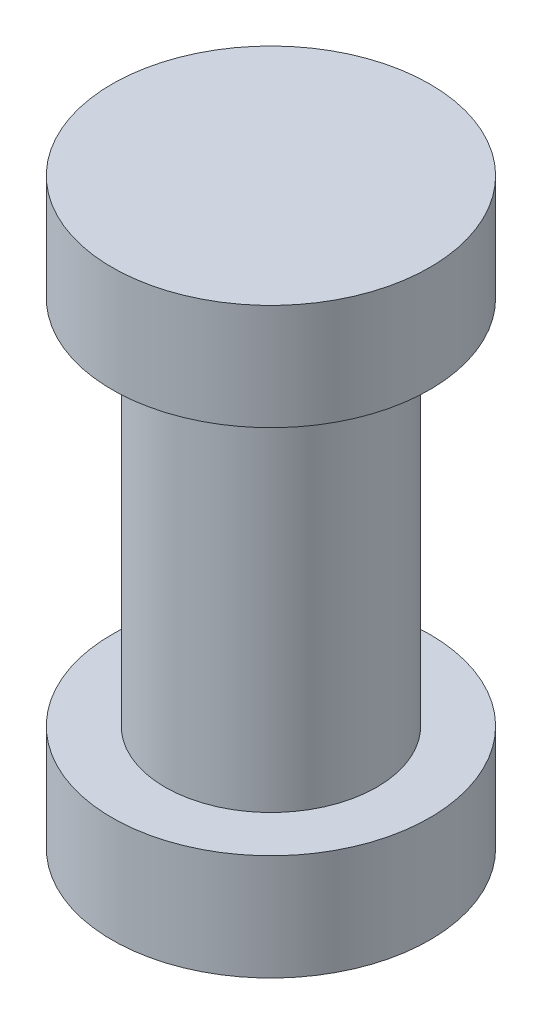
SolidWorks part; units mm, degrees
ref_plane "前视基准面" through (0, 0, 0) normal (0, 0, 1) x (1, 0, 0)
ref_plane "上视基准面" through (0, 0, 0) normal (0, 1, 0) x (1, 0, 0)
ref_plane "右视基准面" through (0, 0, 0) normal (1, 0, 0) x (0, 0, -1)
other "Configuration Table"
sketch "草图1" plane through (0, 0, 0) normal (0, 0, 1) x (1, 0, 0)
  line L0 (0, 2.6518) -> (1.5, 2.6518)
  line L1 (1.5, 2.6518) -> (1.5, 1.6518)
  line L2 (1.5, 1.6518) -> (1, 1.6518)
  line L3 (1, 1.6518) -> (1, -1.8482)
  line L4 (1, -1.8482) -> (1.5, -1.8482)
  line L5 (1.5, -1.8482) -> (1.5, -2.8482)
  line L6 (1.5, -2.8482) -> (0, -2.8482)
  line L7 (0, -2.8482) -> (0, 2.6518)
  dimension "D1" = 1
  dimension "D2" = 1.5
  dimension "D3" = 1
  dimension "D4" = 5.5
  dimension "D5" = 1
  dimension "D6" = 1.5
  dimension "D7" = 0.5
revolve "旋转1" add sketch "草图1" angle 360 about L7
